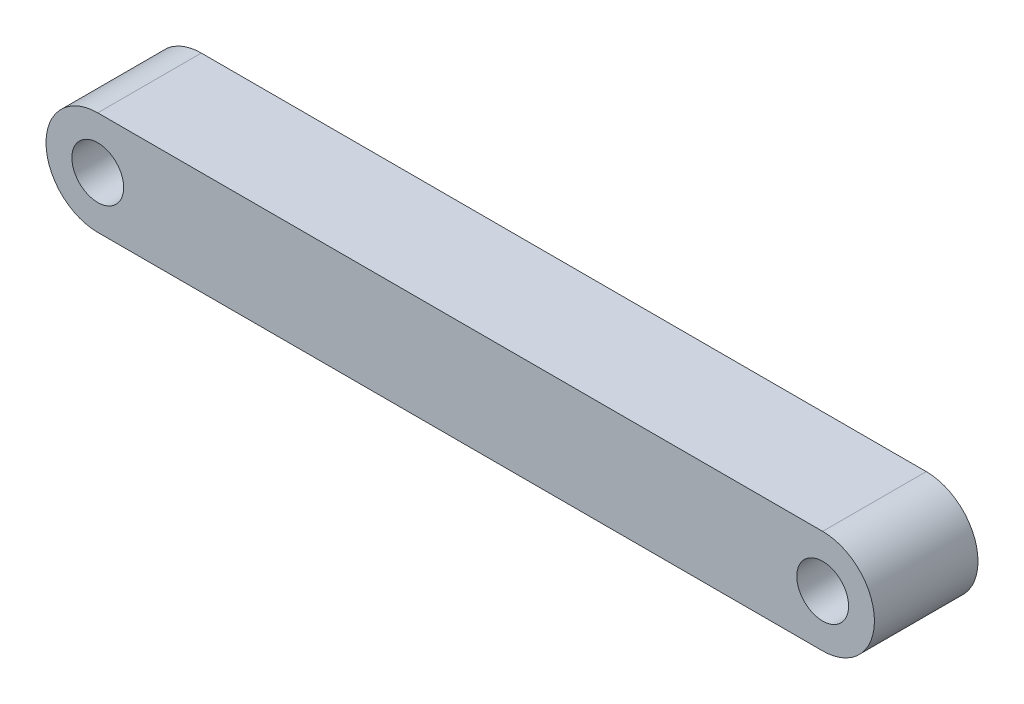
SolidWorks part; units mm, degrees
ref_plane "Front Plane" through (0, 0, 0) normal (0, 0, 1) x (1, 0, 0)
ref_plane "Top Plane" through (0, 0, 0) normal (0, 1, 0) x (1, 0, 0)
ref_plane "Right Plane" through (0, 0, 0) normal (1, 0, 0) x (0, 0, -1)
sketch "Sketch1" plane through (0, 0, 0) normal (0, 0, 1) x (1, 0, 0)
  line L0 (0, 5) -> (-70, 5)
  line L1 (0, 0) -> (-2.5, 0) construction
  line L2 (0, -5) -> (-70, -5)
  line L3 (0, 0) -> (0, -124.2464) construction
  line L4 (-35, 5) -> (-35, -5) construction
  line L5 (-5, 0) -> (-44.6799, 0) construction
  circle A0 centre (0, 0) radius 2.5
  arc A1 (0, -5) -> (0, 5) centre (0, 0) ccw
  circle A2 centre (-61.1518, -66.5797) radius 60 construction
  arc A3 (-70, -5) -> (-70, 5) centre (-70, 0) cw
  circle A4 centre (-70, 0) radius 2.5
  point P5 (0, 2.5)
  dimension "D1" = 5
  dimension "D4" = 70
  dimension "D2" = 2.5
  dimension "D3" = 10
extrude "Boss-Extrude1" add sketch "Sketch1" along normal blind 10
sketch "Sketch2" plane through (0, 0, 10) normal (0, 0, 1) x (1, 0, 0)
  circle A0 centre (0, 0) radius 2.5 construction
  arc A1 (0, -5) -> (0, 5) centre (0, 0) ccw construction
  point P0 (-2.5, 0)
  point P1 (5, 0)
  dimension "D1" = 7.5
